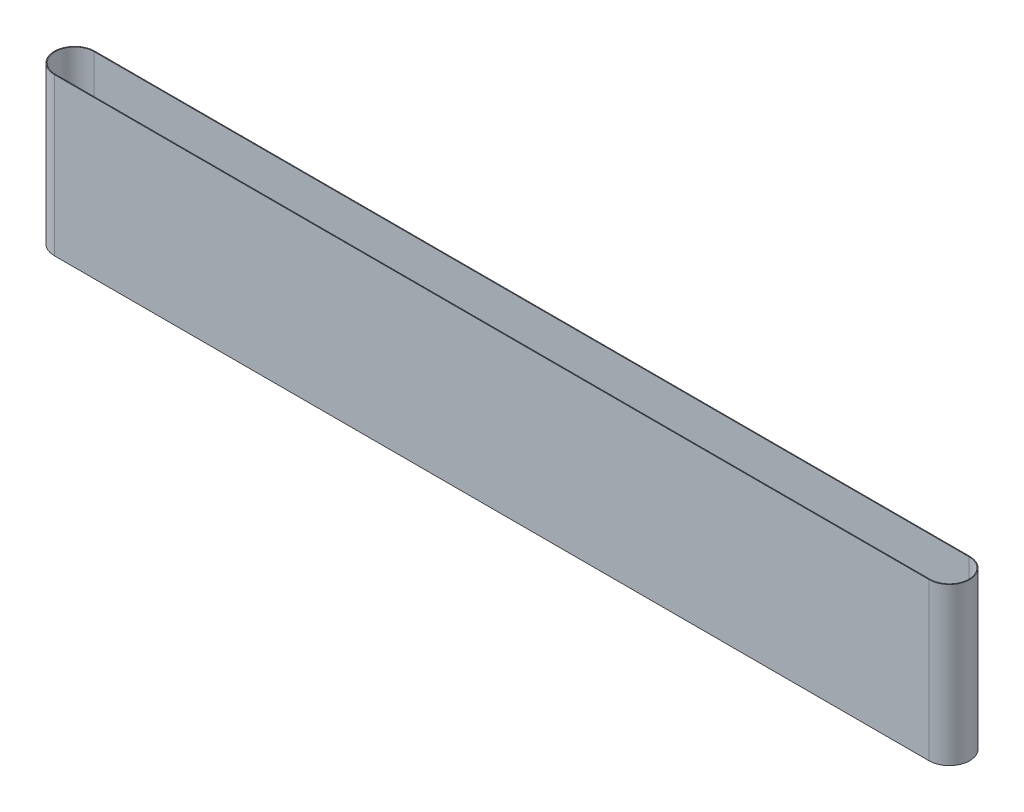
SolidWorks part; units mm, degrees
material "Rubber"
ref_plane "Front Plane" through (0, 0, 0) normal (0, 0, 1) x (1, 0, 0)
ref_plane "Top Plane" through (0, 0, 0) normal (0, 1, 0) x (1, 0, 0)
ref_plane "Right Plane" through (0, 0, 0) normal (1, 0, 0) x (0, 0, -1)
sketch "Sketch1" plane through (0, 0, 0) normal (0, 1, 0) x (1, 0, 0)
  line L0 (-71.1249, 38.8952) -> (1071.6751, 38.8952)
  line L1 (-71.1249, -12.1048) -> (1071.6751, -12.1048)
  arc A0 (-71.1249, 38.8952) -> (-71.1249, -12.1048) centre (-71.1249, 13.3952) ccw
  arc A1 (1071.6751, -12.1048) -> (1071.6751, 38.8952) centre (1071.6751, 13.3952) ccw
  dimension "D1" = 51
  dimension "D2" = 51
  dimension "D3" = 1142.8
extrude "Extrude-Thin1" add sketch "Sketch1" along normal blind 205 thin thin type one direction wall 1
